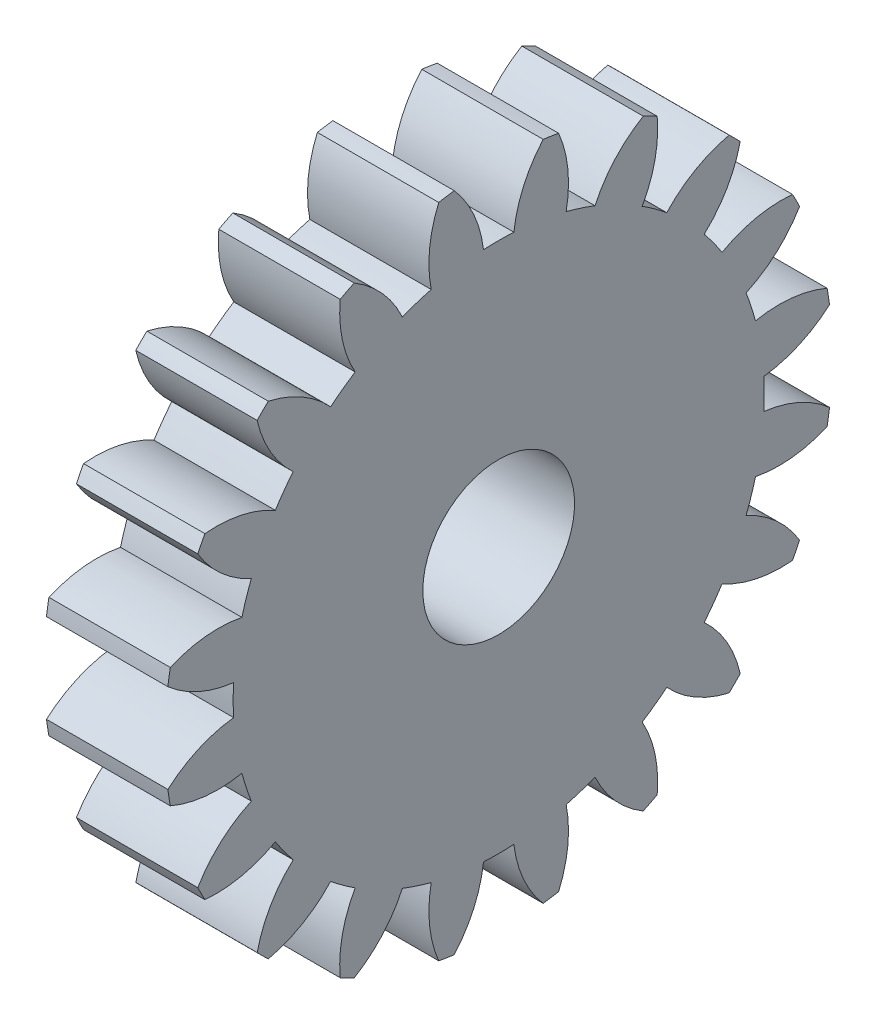
SolidWorks part; units mm, degrees
ref_plane "Plane1" through (0, 0, 0) normal (0, 0, 1) x (1, 0, 0)
ref_plane "Plane2" through (0, 0, 0) normal (0, 1, 0) x (1, 0, 0)
ref_plane "Plane3" through (0, 0, 0) normal (1, 0, 0) x (0, 0, -1)
other "Configuration Table"
sketch "HoldingSke" plane through (0, 0, 0) normal (0, 1, 0) x (1, 0, 0)
  line L0 (0, 0) -> (0.9397, -0.342)
  line L1 (-15, 0) -> (100, 0) construction
  line L2 (0, 0) -> (-2.1039, 2.3779)
  line L3 (0, 0) -> (-11.863, 4.5341)
  line L4 (0, 0) -> (8.1152, 2.9537)
  line L5 (0, 0) -> (-46.8476, -17.4728)
  line L6 (0, 0) -> (-3.3159, -2.2372)
  line L7 (-2.1039, 2.3779) -> (8.6586, 51.2059)
  line L8 (-76.2, 54.61) -> (-75.3, 54.61)
  line L9 (-71.009, 38.7566) -> (-53.1078, 45.2721)
  line L10 (-76.2, 71.12) -> (104.1128, 71.12)
  line L11 (0, 0) -> (-4, 0)
  line L12 (-76.2, 101.6) -> (-76.162, 101.6)
  line L13 (24.9733, 27.94) -> (52.9518, 28.4284)
  line L14 (24.9733, 27.94) -> (24.9743, 27.94)
  line L15 (24.9733, 27.94) -> (100.4006, 29.5858)
  line L16 (-63.627, -1) -> (-12.827, -1)
  circle A0 centre (0, 0) radius 2.5
  circle A1 centre (0, 0) radius 8.749
  circle A2 centre (0, 0) radius 37.5
  circle A3 centre (0, 0) radius 2.5
  dimension "MHD" = 17.498
  dimension "Hub_dia" = 75
  dimension "Bore" = 5
  dimension "MBD" = 5
  dimension "Num_teeth" = 20
  dimension "Pitch" = 1
  dimension "Overall_len" = 50
  dimension "Show_teeth" = 20
  dimension "Thickness" = 4
  dimension "OAL" = 50.0001
  dimension "T_dim" = 0.9
  dimension "Ap" = 20
  dimension "H" = 19.05
  dimension "Pitch_radius" = 180.3128
  dimension "Width" = 4
  dimension "Backlash" = 0.038
  dimension "Addendum_fac" = 1
  dimension "Dedendum_fac" = 1.25
  dimension "Clearance_fac" = 0.25
  dimension "Dedendum_add" = 0.001
  dimension "Module" = 1
sketch "BasProSke" plane through (0, 0, 0) normal (0, 1, 0) x (1, 0, 0)
  line L0 (-10, 0) -> (60, 0) construction
  line L1 (0, 0) -> (0, 11)
  line L2 (0, 0) -> (4, 0)
  line L3 (4, 0) -> (4, 11)
  line L4 (4, 11) -> (0, 11)
  dimension "Thickness" = 4
  dimension "Diameter" = 22
revolve "Base-Revolve" add sketch "BasProSke" angle 360 about L0
sketch "TooCutSke" plane through (0, 0, 0) normal (1, 0, 0) x (0, 0, -1)
  line L1 (0, 0) -> (0, 107) construction
  line L2 (0, 0) -> (-0.8511, 9.9637) construction
  line L3 (0, 0) -> (-3.1206, 19.7028) construction
  line L4 (-0.8511, 9.9637) -> (-1.5603, 9.8514) construction
  arc A0 (0.4999, 8.7347) -> (-0.4999, 8.7347) centre (0, 0) ccw
  arc A1 (1.4852, 10.9249) -> (-1.4852, 10.9249) centre (0, 0) ccw
  circle A2 centre (0, 0) radius 10 construction
  circle A3 centre (0, 0) radius 9.3969 construction
  arc A4 (-0.4999, 8.7347) -> (-1.4852, 10.9249) centre (-4.4722, 8.2645) ccw
  arc A5 (1.4852, 10.9249) -> (0.4999, 8.7347) centre (4.4722, 8.2645) ccw
  dimension "Root_dia" = 17.498
  dimension "Overcut_dia" = 22.0508
  dimension "Pitch_dia" = 20
  dimension "Base_dia" = 18.7939
  dimension "Flank_rad" = 4
  dimension "Half_ang" = 9
  dimension "Half_CT" = 0.7181
extrude "ToothCut" cut sketch "TooCutSke" along normal through all
fillet "Breaks" [suppressed] radius 0.02
fillet "RootFillets" [suppressed] radius 0.251
pattern_circular "TeethCuts" count 20 every 18 about axis through (-10, 0, 0) along (1, 0, 0) of "ToothCut", "RootFillets", "Breaks"
sketch "HubNeaOneSke" plane through (0, 0, 0) normal (-1, 0, 0) x (0, 0, 1)
  circle A0 centre (0, 0) radius 8.749
  dimension "Diameter" = 17.498
extrude "HubNearOne" [suppressed] add sketch "HubNeaOneSke" along normal blind 46.0001
sketch "HubNeaBotSke" plane through (0, 0, 0) normal (-1, 0, 0) x (0, 0, 1)
  circle A0 centre (0, 0) radius 8.749
  dimension "Diameter" = 17.498
extrude "HubNearBoth" [suppressed] add sketch "HubNeaBotSke" along normal blind 23
ref_plane "FarPln" through (4, 0, 0) normal (1, 0, 0) x (0, 0, -1)
sketch "HubFarSke" plane through (4, 0, 0) normal (1, 0, 0) x (0, 0, -1)
  circle A0 centre (0, 0) radius 8.749
  dimension "Diameter" = 17.498
extrude "HubFar" [suppressed] add sketch "HubFarSke" along normal blind 23
sketch "BorSke" plane through (0, 0, 0) normal (1, 0, 0) x (0, 0, -1)
  circle A0 centre (0, 0) radius 2.5
  dimension "Diameter" = 5
extrude "Bore" cut sketch "BorSke" along normal mid plane 100.0001
sketch "KeySke" plane through (0, 0, 0) normal (1, 0, 0) x (0, 0, -1)
  line L0 (-1, 0) -> (-1, 3.4)
  line L1 (-1, 3.4) -> (1, 3.4)
  line L2 (1, 3.4) -> (1, 0)
  line L3 (0, 0) -> (0, 34) construction
  line L4 (-1, 0) -> (1, 0)
  dimension "Offset" = 3.4
  dimension "Width" = 2
extrude "Keyway" [suppressed] cut sketch "KeySke" along normal mid plane 100.0001
pattern_circular "Keyway2" [suppressed] count 2 every 90 about axis through (-10, 0, 0) along (1, 0, 0)
equation "' \"Module@HoldingSke\" = 6.35"
equation "' \"Num_teeth@HoldingSke\" = 12"
equation "' \"Ap@HoldingSke\" =  20"
equation "' \"Ap@HoldingSke\" = 20"
equation "' \"Width@HoldingSke\" = 0.5 * 25.4"
equation "' \"Hub_dia@HoldingSke\"= 1 * 25.4"
equation "' \"Hub_dia@HoldingSke\" = 1 * 25.4"
equation "' \"Overall_len@HoldingSke\" = 1.0 * 25.4"
equation "' \"Bore@HoldingSke\" = 0.75 * 25.4"
equation "' \"T_dim@HoldingSke\" = 0.1 * 25.4"
equation "' \"Width@KeySke\" = 0.25 * 25.4"
equation "' \"Show_teeth@HoldingSke\" = 13"
equation "' \"Backlash@HoldingSke\" = 0.009 * 25.4"
equation "' \"Addendum_fac@HoldingSke\" = 1.0"
equation "' \"Dedendum_fac@HoldingSke\" = 1.25"
equation "' \"Dedendum_add@HoldingSke\" = 0.00005 * 25.4"
equation "' \"Clearance_fac@HoldingSke\" = 0.25"
equation "\"Pitch@HoldingSke\" = 1 / \"Module@HoldingSke\""
equation "\"Overcut_dia@TooCutSke\" = (\"Num_teeth@HoldingSke\" + 2 * \"Addendum_fac@HoldingSke\") / \"Pitch@HoldingSke\" + 0.002 * 25.4"
equation "\"Pitch_dia@TooCutSke\" = \"Num_teeth@HoldingSke\" / \"Pitch@HoldingSke\""
equation "\"Base_dia@TooCutSke\" = \"Num_teeth@HoldingSke\" / \"Pitch@HoldingSke\" * cos((\"Ap@HoldingSke\"  * 3.14159265 / 180))"
equation "\"Root_dia@TooCutSke\" = (\"Num_teeth@HoldingSke\" + 2) / \"Pitch@HoldingSke\" - 2 * (\"Addendum_fac@HoldingSke\" + \"Dedendum_fac@HoldingSke\") / \"Pitch@HoldingSke\" - \"Dedendum_add@HoldingSke\" * 2"
equation "\"Half_ang@TooCutSke\" = 180 / \"Num_teeth@HoldingSke\""
equation "\"Half_CT@TooCutSke\" = \"Num_teeth@HoldingSke\" / \"Pitch@HoldingSke\" * sin((3.14159265 / 2 / \"Num_teeth@HoldingSke\")) / 2 - 7 * \"Backlash@HoldingSke\" / 4"
equation "\"Flank_rad@TooCutSke\" = \"Num_teeth@HoldingSke\" / \"Pitch@HoldingSke\" / 5"
equation "\"Radius@RootFillets\" = \"Clearance_fac@HoldingSke\" / \"Pitch@HoldingSke\" + \"Dedendum_add@HoldingSke\""
equation "\"Break_rad@Breaks\" = 0.02 / \"Pitch@HoldingSke\""
equation "\"Thickness@HoldingSke\" = \"Width@HoldingSke\""
equation "\"OAL@HoldingSke\" = \"Thickness@HoldingSke\""
equation "\"MHD@HoldingSke\" = (\"Num_teeth@HoldingSke\" + 2) / \"Pitch@HoldingSke\" - 2 * (\"Addendum_fac@HoldingSke\" + \"Dedendum_fac@HoldingSke\")  / \"Pitch@HoldingSke\" - \"Dedendum_add@HoldingSke\" * 2"
equation "\"MBD@HoldingSke\" = (\"Num_teeth@HoldingSke\" + 2) / \"Pitch@HoldingSke\" - 2 * (\"Addendum_fac@HoldingSke\" + \"Dedendum_fac@HoldingSke\")  / \"Pitch@HoldingSke\" - \"Dedendum_add@HoldingSke\" * 2 - 0.002 * 25.4"
equation "\"MHD@HoldingSke\" = ((sgn( \"MHD@HoldingSke\" - \"Hub_dia@HoldingSke\" )-1)*( \"MHD@HoldingSke\" - \"Hub_dia@HoldingSke\" ))/-2+ \"Hub_dia@HoldingSke\""
equation "\"MBD@HoldingSke\" = ((sgn( \"MBD@HoldingSke\" - \"Bore@HoldingSke\" )-1)*( \"MBD@HoldingSke\" - \"Bore@HoldingSke\" ))/-2+ \"Bore@HoldingSke\""
equation "\"OAL@HoldingSke\" = ((sgn( \"OAL@HoldingSke\" - \"Overall_len@HoldingSke\" )+1)*( \"OAL@HoldingSke\" - \"Overall_len@HoldingSke\" ))/2 + \"Overall_len@HoldingSke\" + 0.000002 * 25.4"
equation "\"Num_teeth@TeethCuts\" = int( \"Show_teeth@HoldingSke\" ) + 1"
equation "\"Num_teeth@TeethCuts\" = ((sgn( \"Num_teeth@TeethCuts\" - \"Num_teeth@HoldingSke\" )-1)*( \"Num_teeth@TeethCuts\" - \"Num_teeth@HoldingSke\" ))/-2+ \"Num_teeth@HoldingSke\""
equation "\"Num_teeth@TeethCuts\" = ((sgn( \"Num_teeth@TeethCuts\" - 2.0)+1)*( \"Num_teeth@TeethCuts\" - 2.0))/2 +2.0"
equation "\"Angle@TeethCuts\" = 360.0 / \"Num_teeth@HoldingSke\""
equation "\"Diameter@BasProSke\" = (\"Num_teeth@HoldingSke\" + 2 * \"Addendum_fac@HoldingSke\") / \"Pitch@HoldingSke\""
equation "\"Thickness@BasProSke\"  = \"Thickness@HoldingSke\""
equation "' \"Fillet_rad@BasProSke\" =  \"Thickness@HoldingSke\" * 0.05"
equation "' \"Fillet_rad@BasProSke\" = \"Thickness@HoldingSke\" * 0.05"
equation "\"MHD@HoldingSke\" = ((sgn( \"MHD@HoldingSke\" - \"Root_dia@TooCutSke\" )-1)*( \"MHD@HoldingSke\" - \"Root_dia@TooCutSke\" ))/-2+ \"Root_dia@TooCutSke\""
equation "\"Diameter@HubNeaOneSke\" = \"MHD@HoldingSke\""
equation "\"Length@HubNearOne\" = \"OAL@HoldingSke\" - \"Thickness@BasProSke\""
equation "\"Diameter@HubNeaBotSke\" = \"MHD@HoldingSke\""
equation "\"Length@HubNearBoth\" = ( \"OAL@HoldingSke\" - \"Thickness@BasProSke\" ) / 2.0"
equation "\"Thickness@FarPln\" = \"Thickness@BasProSke\""
equation "\"Diameter@HubFarSke\" = \"MHD@HoldingSke\""
equation "\"Length@HubFar\" = ( \"OAL@HoldingSke\" - \"Thickness@BasProSke\" ) / 2.0"
equation "\"Diameter@BorSke\" = \"MBD@HoldingSke\""
equation "\"D1@Bore\" = \"OAL@HoldingSke\" * 2.0"
equation "\"D1@Keyway\" = \"OAL@HoldingSke\" * 2.0"
equation "\"Offset@KeySke\" = \"T_dim@HoldingSke\" + \"MBD@HoldingSke\" / 2.0"
